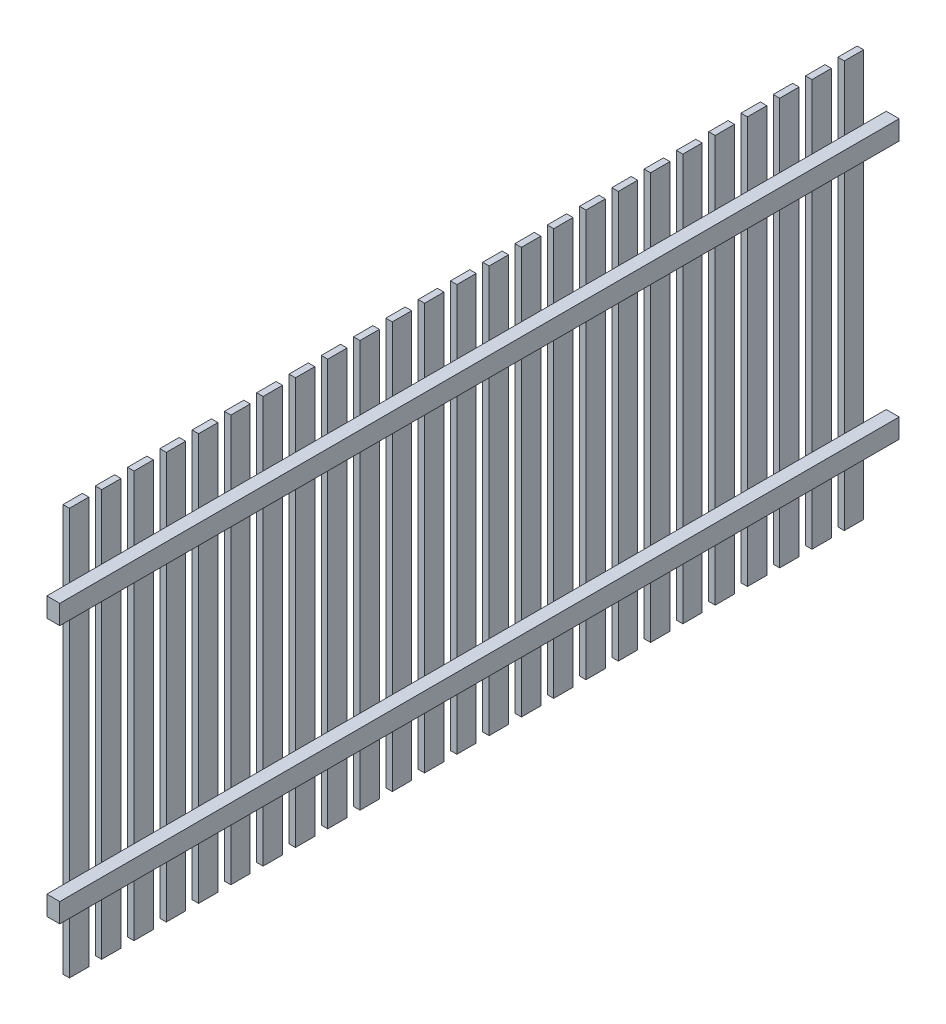
SolidWorks part; units mm, degrees
ref_plane "Vorderansicht" through (0, 0, 0) normal (0, 0, 1) x (1, 0, 0)
ref_plane "Draufsicht" through (0, 0, 0) normal (0, 1, 0) x (1, 0, 0)
ref_plane "Seitenansicht" through (0, 0, 0) normal (1, 0, 0) x (0, 0, -1)
sketch "Skizze1" plane through (0, 0, 0) normal (0, 0, 1) x (1, 0, 0)
  line L1 (0, 0) -> (40, 0)
  line L2 (0, 0) -> (0, 60)
  line L3 (0, 60) -> (40, 60)
  line L4 (40, 0) -> (40, 60)
  dimension "D1" = 40
  dimension "D2" = 60
extrude "Aufsatz-Linear austragen1" add sketch "Skizze1" along normal mid plane 2600
pattern_linear "Lineares Muster1" count 2 spacing 800 along (0, 1, 0) of "Aufsatz-Linear austragen1"
sketch "Skizze2" plane through (0, 0, 0) normal (-1, 0, 0) x (0, 0, 1)
  line L0 (0, 0) -> (0, -200) construction
  line L1 (-30, 1060) -> (30, 1060)
  line L2 (-30, 1060) -> (-30, -200)
  line L3 (-30, -200) -> (30, -200)
  line L4 (30, 1060) -> (30, -200)
  line L5 (1300, 0) -> (-1300, 0) construction
  line L6 (1300, 860) -> (-1300, 860) construction
  dimension "D1" = 200
  dimension "D2" = 60
  dimension "D3" = 200
extrude "Aufsatz-Linear austragen2" add sketch "Skizze2" along normal blind 20 separate body
pattern_linear "Lineares Muster2" count 13 spacing 100 along (0, 0, 1) count 13 spacing 100 along (0, 0, -1) of bodies 103
equation "\"D2@Lineares Muster2\" = ( \"D1@Aufsatz-Linear austragen1\" / \"D3@Lineares Muster2\" ) / 2"
equation "\"D1@Lineares Muster2\"= ( \"D1@Aufsatz-Linear austragen1\" / \"D3@Lineares Muster2\" ) / 2"
